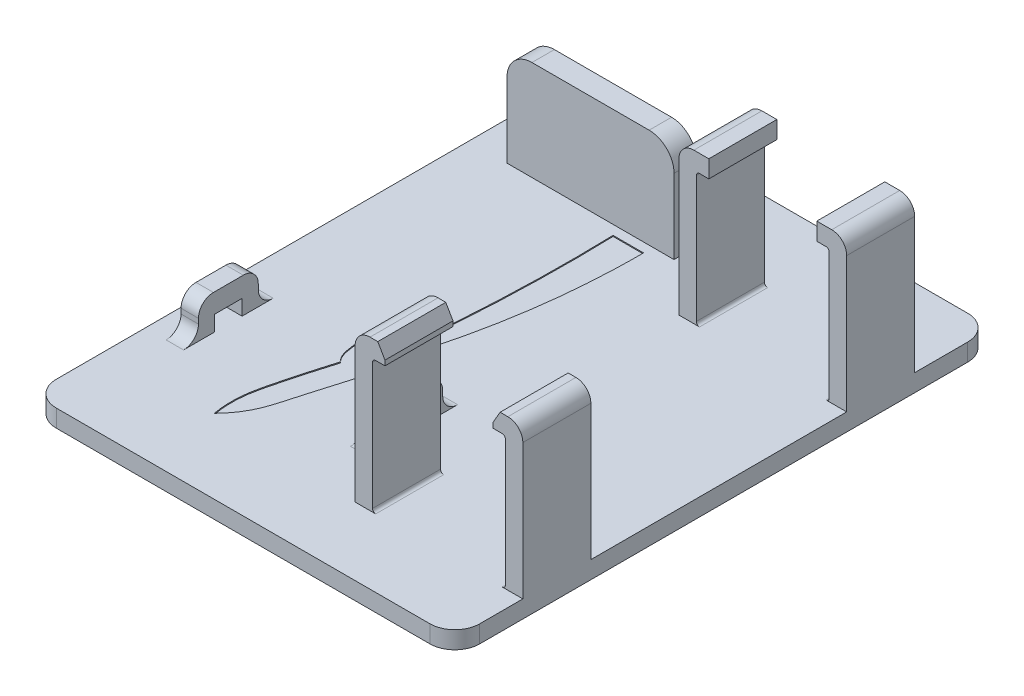
SolidWorks part; units mm, degrees
ref_plane "Front" through (0, 0, 0) normal (0, 0, 1) x (1, 0, 0)
ref_plane "Top" through (0, 0, 0) normal (0, 1, 0) x (1, 0, 0)
ref_plane "Right" through (0, 0, 0) normal (1, 0, 0) x (0, 0, -1)
sketch "Sketch1" plane through (0, 0, 0) normal (0, 1, 0) x (1, 0, 0)
  line L1 (-40.4961, 57.2584) -> (34.5039, 57.2584)
  line L2 (-45.4961, 52.2584) -> (-45.4961, -45.6916)
  line L3 (-40.4961, -50.6916) -> (34.5039, -50.6916)
  line L4 (39.5039, 52.2584) -> (39.5039, -45.6916)
  arc A0 (34.5039, -50.6916) -> (39.5039, -45.6916) centre (34.5039, -45.6916) ccw
  arc A1 (-45.4961, -45.6916) -> (-40.4961, -50.6916) centre (-40.4961, -45.6916) ccw
  arc A2 (-40.4961, 57.2584) -> (-45.4961, 52.2584) centre (-40.4961, 52.2584) ccw
  arc A3 (34.5039, 57.2584) -> (39.5039, 52.2584) centre (34.5039, 52.2584) cw
  point P8 (-45.4961, -50.6916)
  point P11 (-45.4961, 57.2584)
  point P14 (39.5039, 57.2584)
  dimension "D3" = 5
  dimension "D1" = 107.95
  dimension "D2" = 85
extrude "Boss-Extrude1" add sketch "Sketch1" along normal blind 3.5 contours L1 A3 L4 A0 L3 A1 L2 A2
sketch "Sketch2" plane through (0, 3.5, 0) normal (0, 1, 0) x (1, 0, 0)
  line L0 (39.5039, 52.2584) -> (39.5039, -45.6916) construction
  line L1 (39.5039, -37.0429) -> (36.0039, -37.0429)
  line L2 (39.5039, -37.0429) -> (39.5039, -23.3901)
  line L3 (39.5039, -23.3901) -> (36.0039, -23.3901)
  line L4 (36.0039, -37.0429) -> (36.0039, -23.3901)
  line L6 (9.3339, -37.0429) -> (5.8339, -37.0429)
  line L7 (9.3339, -37.0429) -> (9.3339, -23.3901)
  line L8 (9.3339, -23.3901) -> (5.8339, -23.3901)
  line L9 (5.8339, -37.0429) -> (5.8339, -23.3901)
  dimension "D1" = 3.5
  dimension "D2" = 3.5
  dimension "D3" = 26.67
extrude "Boss-Extrude2" add sketch "Sketch2" along normal blind 26.67
sketch "Sketch3" plane through (0, 30.17, 0) normal (0, 1, 0) x (1, 0, 0)
  line L0 (5.8339, -23.3901) -> (5.8339, -37.0429) construction
  line L1 (5.8339, -23.3901) -> (11.8339, -23.3901)
  line L2 (5.8339, -23.3901) -> (5.8339, -37.0429)
  line L3 (5.8339, -37.0429) -> (11.8339, -37.0429)
  line L4 (11.8339, -23.3901) -> (11.8339, -37.0429)
  line L6 (39.5039, -37.0429) -> (33.5039, -37.0429)
  line L7 (39.5039, -37.0429) -> (39.5039, -23.3901)
  line L8 (39.5039, -23.3901) -> (33.5039, -23.3901)
  line L9 (33.5039, -37.0429) -> (33.5039, -23.3901)
  dimension "D1" = 6
  dimension "D2" = 6
extrude "Boss-Extrude3" add sketch "Sketch3" along normal blind 3.5
chamfer "Chamfer1" distance 2.5 angle 30 2 edges at (33.5039, 33.67, 30.2165) (11.8339, 33.67, 30.2165)
fillet "Fillet1" radius 3 2 edges at (39.5039, 33.67, 30.2165) (5.8339, 33.67, 30.2165)
fillet "Fillet2" radius 0.635 4 edges at (36.0039, 3.5, 30.2165) (9.3339, 3.5, 30.2165) (36.0039, 30.17, 30.2165) (9.3339, 30.17, 30.2165)
pattern_linear "LPattern1" count 2 spacing 65 along (0, 0, -1) of "Boss-Extrude2", "Fillet1", "Boss-Extrude3", "Fillet2"
sketch "Sketch4" plane through (0, 3.5, 0) normal (0, 1, 0) x (1, 0, 0)
  line L0 (9.9689, 41.6099) -> (5.8339, 41.6099) construction
  line L1 (-37.816, 37.1099) -> (-4.2976, 37.1099)
  line L2 (-37.816, 37.1099) -> (-37.816, 41.6099)
  line L3 (-37.816, 41.6099) -> (-4.2976, 41.6099)
  line L4 (-4.2976, 37.1099) -> (-4.2976, 41.6099)
  dimension "D1" = 0
  dimension "D2" = 4.5
extrude "Boss-Extrude4" add sketch "Sketch4" along normal blind 20
fillet "Fillet3" radius 3 1 edges at (-21.0568, 3.5, -41.6099)
fillet "Fillet4" radius 5 2 edges at (-4.2976, 23.5, -39.3599) (-37.816, 23.5, -39.3599)
sketch "Sketch5" plane through (0, 3.5, 0) normal (0, 1, 0) x (1, 0, 0)
  line L0 (-15.2817, -10.8882) -> (-14.6255, -8.282)
  line L1 (-14.6255, -8.282) -> (-17.0255, -7.5789)
  line L2 (-17.0255, -7.5789) -> (-17.7005, -10.1476)
  line L3 (-8.5261, 35.2116) -> (-14.6379, 35.2113)
  line L4 (-16.4881, -7.7041) -> (-15.038, -8.129)
  spline S0 degree 3 poles (-24.038, -32.8539) (-23.9922, -33.828) (-23.886, -34.7984) (-23.72, -35.7594) knots 0 0 0 0 1 1 1 1
  spline S1 degree 3 poles (-23.72, -35.7594) (-22.884, -34.8934) (-22.1288, -33.9529) (-21.464, -32.9495) knots 1 1 1 1 2 2 2 2
  spline S2 degree 3 poles (-21.464, -32.9495) (-19.5661, -30.083) (-19.1686, -27.6995) (-17.738, -22.8039) knots 2 2 2 2 3 3 3 3
  spline S3 degree 3 poles (-17.738, -22.8039) (-17.3686, -21.5409) (-16.6104, -18.9507) (-15.5536, -15.3789) knots 3 3 3 3 4 4 4 4
  spline S4 degree 3 poles (-15.5536, -15.3789) (-15.3894, -15.3591) (-15.2266, -15.3291) (-15.0661, -15.2889) knots 4 4 4 4 5 5 5 5
  spline S5 degree 3 poles (-15.0661, -15.2889) (-13.9295, -15.0046) (-13.0602, -14.243) (-11.3356, -11.9382) knots 5 5 5 5 6 6 6 6
  spline S6 degree 3 poles (-11.3356, -11.9382) (-10.8267, -11.2584) (-10.1975, -10.382) (-9.5075, -9.332) knots 6 6 6 6 7 7 7 7
  spline S7 degree 3 poles (-9.5075, -9.332) (-10.1749, -9.6714) (-10.86, -9.975) (-11.5599, -10.2414) knots 7 7 7 7 8 8 8 8
  spline S8 degree 3 poles (-11.5599, -10.2414) (-13.1697, -10.8534) (-13.925, -10.9111) (-14.213, -10.9257) knots 8 8 8 8 9 9 9 9
  spline S9 degree 3 poles (-14.213, -10.9257) (-14.5697, -10.9436) (-14.9272, -10.9311) (-15.2817, -10.8882) knots 9 9 9 9 10 10 10 10
  spline S10 degree 3 poles (-17.7005, -10.1476) (-19.3965, -9.0806) (-20.7376, -7.534) (-21.5536, -5.7039) knots 13 13 13 13 14 14 14 14
  spline S11 degree 3 poles (-21.5536, -5.7039) (-21.7033, -7.1973) (-21.697, -8.7023) (-21.5349, -10.1945) knots 14 14 14 14 15 15 15 15
  spline S12 degree 3 poles (-21.5349, -10.1945) (-21.3155, -12.1895) (-20.912, -13.2114) (-20.1567, -13.9632) knots 15 15 15 15 16 16 16 16
  spline S13 degree 3 poles (-20.1567, -13.9632) (-20.0919, -14.0277) (-20.036, -14.0787) (-19.9974, -14.1132) knots 16 16 16 16 17 17 17 17
  spline S14 degree 3 poles (-19.9974, -14.1132) (-20.8974, -17.1039) (-21.6571, -19.8061) (-22.2879, -22.154) knots 17 17 17 17 18 18 18 18
  spline S15 degree 3 poles (-22.2879, -22.154) (-23.7005, -27.4081) (-24.1809, -29.8141) (-24.038, -32.8539) knots 18 18 18 18 19 19 19 19
  spline S16 degree 3 poles (-14.6379, 35.2113) (-14.4331, 28.1031) (-14.4669, 20.4813) (-14.8505, 12.4083) knots 1 1 1 1 2 2 2 2
  spline S17 degree 3 poles (-14.8505, 12.4083) (-15.1876, 5.3133) (-15.7602, -1.4041) (-16.4881, -7.7041) knots 2 2 2 2 3 3 3 3
  spline S18 degree 3 poles (-15.038, -8.129) (-10.6568, 5.8983) (-8.4604, 20.5162) (-8.5261, 35.2116) knots 4 4 4 4 5 5 5 5
extrude "Cut-Extrude1" cut sketch "Sketch5" against normal blind 0.2
sketch "Sketch6" plane through (0, 3.5, 0) normal (0, 1, 0) x (1, 0, 0)
  line L0 (-4.2976, 37.1099) -> (-4.2976, 44.6099) construction
  line L1 (-4.2976, -24.8254) -> (-0.7976, -24.8254)
  line L2 (-4.2976, -24.8254) -> (-4.2976, -12.8254)
  line L3 (-4.2976, -12.8254) -> (-0.7976, -12.8254)
  line L4 (-0.7976, -24.8254) -> (-0.7976, -12.8254)
  line L5 (-41.316, -24.8254) -> (-37.816, -24.8254)
  line L6 (-41.316, -24.8254) -> (-41.316, -12.8254)
  line L7 (-41.316, -12.8254) -> (-37.816, -12.8254)
  line L8 (-37.816, -24.8254) -> (-37.816, -12.8254)
  line L9 (-37.816, 44.6099) -> (-37.816, 37.1099) construction
  point P12 (-2.5476, -24.8254)
  dimension "D1" = 3.5
  dimension "D2" = 3.5
  dimension "D3" = 12
  dimension "D4" = 12
  dimension "D5" = 0
  dimension "D6" = 0
  dimension "D7" = 0
extrude "Boss-Extrude5" add sketch "Sketch6" along normal blind 7
fillet "Fillet5" radius 3 8 edges at (-2.5476, 3.5, 24.8254) (-2.5476, 10.5, 12.8254) (-2.5476, 3.5, 12.8254) (-39.566, 3.5, 12.8254) (-39.566, 3.5, 24.8254) (-2.5476, 10.5, 24.8254) (-39.566, 10.5, 12.8254) (-39.566, 10.5, 24.8254)
sketch "Sketch7" plane through (-0.7976, 0, 0) normal (1, 0, 0) x (0, 0, -1)
  line L0 (-27.8254, 3.5) -> (-9.8254, 3.5) construction
  line L1 (-21.5754, 3.5) -> (-16.0754, 3.5)
  line L2 (-21.5754, 3.5) -> (-21.5754, 6.594)
  line L3 (-21.5754, 6.594) -> (-16.0754, 6.594)
  line L4 (-16.0754, 3.5) -> (-16.0754, 6.594)
  line L5 (-21.8254, 10.5) -> (-15.8254, 10.5) construction
  point P6 (-18.8254, 6.594)
  point P9 (-18.8254, 10.5)
  dimension "D1" = 5.5
  dimension "D2" = 0
extrude "Cut-Extrude2" cut sketch "Sketch7" against normal through all
